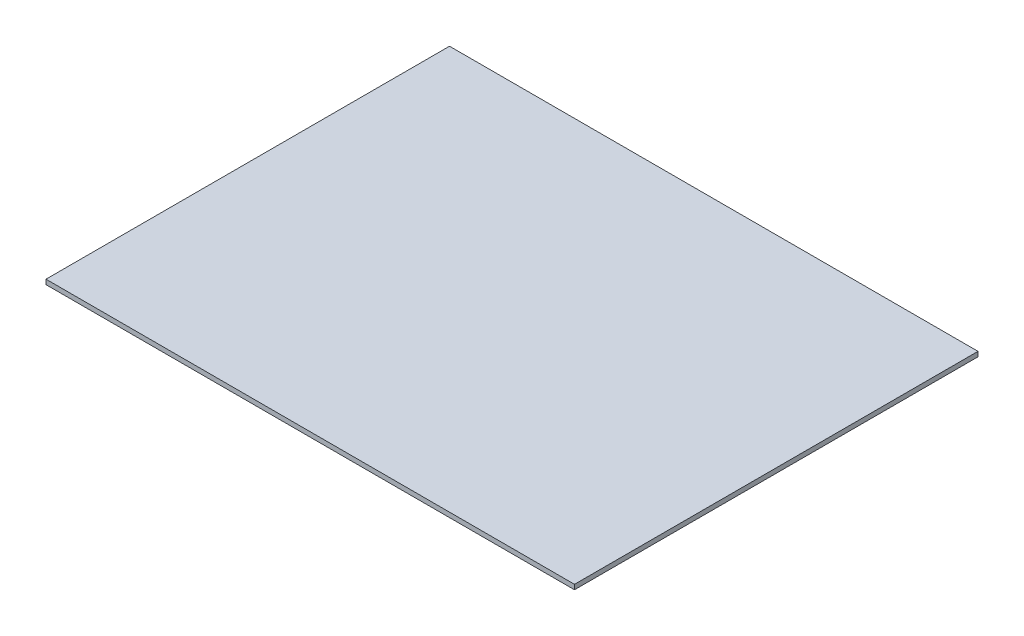
SolidWorks part; units mm, degrees
ref_plane "Спереди" through (0, 0, 0) normal (0, 0, 1) x (1, 0, 0)
ref_plane "Сверху" through (0, 0, 0) normal (0, 1, 0) x (1, 0, 0)
ref_plane "Справа" through (0, 0, 0) normal (1, 0, 0) x (0, 0, -1)
sketch "Эскиз1" plane through (0, 0, 0) normal (0, 1, 0) x (1, 0, 0)
  line L1 (-222, -169.5) -> (222, -169.5)
  line L2 (-222, -169.5) -> (-222, 169.5)
  line L3 (-222, 169.5) -> (222, 169.5)
  line L4 (222, -169.5) -> (222, 169.5)
  line L5 (-222, -169.5) -> (222, 169.5) construction
  line L6 (-222, 169.5) -> (222, -169.5) construction
  point P0 (0, 0)
  dimension "D1" = 339
  dimension "D2" = 444
extrude "Бобышка-Вытянуть1" add sketch "Эскиз1" along normal blind 4
